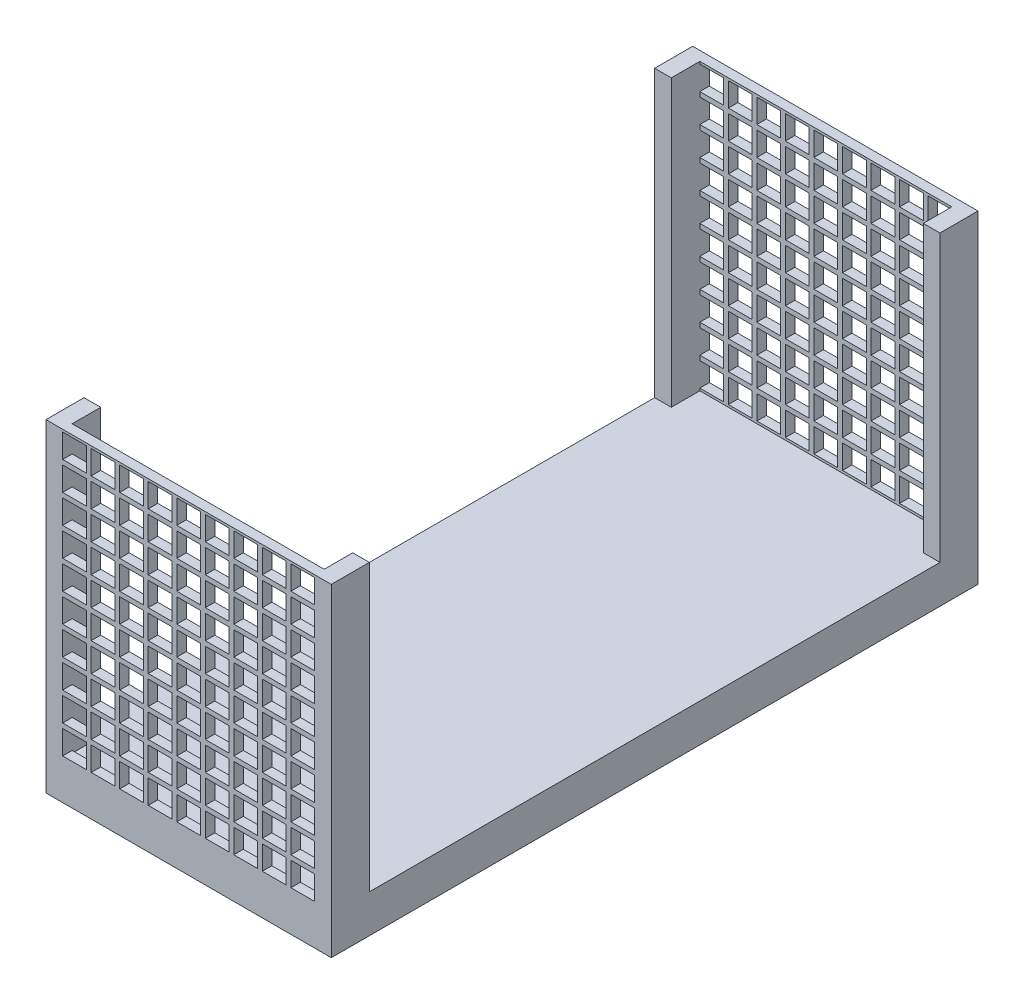
SolidWorks part; units mm, degrees
ref_plane "Front Plane" through (0, 0, 0) normal (0, 0, 1) x (1, 0, 0)
ref_plane "Top Plane" through (0, 0, 0) normal (0, 1, 0) x (1, 0, 0)
ref_plane "Right Plane" through (0, 0, 0) normal (1, 0, 0) x (0, 0, -1)
sketch "Sketch1" plane through (0, 0, 0) normal (0, 0, 1) x (1, 0, 0)
  line L1 (7.5, -8.5) -> (-7.5, -8.5)
  line L2 (7.5, -8.5) -> (7.5, 8.5)
  line L3 (7.5, 8.5) -> (-7.5, 8.5)
  line L4 (-7.5, -8.5) -> (-7.5, 8.5)
  line L5 (7.5, -8.5) -> (-7.5, 8.5) construction
  line L6 (7.5, 8.5) -> (-7.5, -8.5) construction
  point P0 (0, 0)
  dimension "D1" = 15
  dimension "D2" = 17
extrude "Boss-Extrude1" add sketch "Sketch1" along normal blind 34
sketch "Sketch2" plane through (7.5, 0, 0) normal (1, 0, 0) x (0, 0, -1)
  line L0 (-34, 8.5) -> (0, 8.5) construction
  line L1 (-32, 8.5) -> (-2, 8.5)
  line L2 (-32, 8.5) -> (-32, -6.5)
  line L3 (-32, -6.5) -> (-2, -6.5)
  line L4 (-2, 8.5) -> (-2, -6.5)
  line L5 (-34, -8.5) -> (-34, 8.5) construction
  line L6 (-34, -8.5) -> (0, -8.5) construction
  line L7 (0, -8.5) -> (0, 8.5) construction
  dimension "D1" = 2
  dimension "D2" = 2
  dimension "D3" = 2
extrude "Cut-Extrude1" cut sketch "Sketch2" against normal up to next
sketch "Sketch5" plane through (0, 0, 0) normal (0, 0, -1) x (-1, 0, 0)
  line L0 (-7.5, 8.5) -> (7.5, 8.5) construction
  line L1 (-6.625, 8.5) -> (6.625, 8.5)
  line L2 (-6.625, 8.5) -> (-6.625, -6.5)
  line L3 (-6.625, -6.5) -> (6.625, -6.5)
  line L4 (6.625, 8.5) -> (6.625, -6.5)
  line L5 (-6.625, 8.5) -> (-7.5, 8.5) construction
  line L6 (-7.5, 8.5) -> (6.625, 8.5) construction
  line L7 (-7.5, -8.5) -> (-7.5, 8.5) construction
  line L8 (6.625, 8.5) -> (7.5, 8.5) construction
  line L9 (7.5, -8.5) -> (-7.5, -8.5) construction
  dimension "D1" = 0.875
  dimension "D2" = 2
extrude "Cut-Extrude4" cut sketch "Sketch5" along normal blind 1.5 from surface at -2 starting at face at (0, 1, 2)
sketch "Sketch3" plane through (0, 0, 34) normal (0, 0, 1) x (1, 0, 0)
  line L0 (7.5, 8.5) -> (-7.5, 8.5) construction
  line L1 (-6.625, 8.5) -> (6.625, 8.5)
  line L2 (-6.625, 8.5) -> (-6.625, -6.5)
  line L3 (-6.625, -6.5) -> (6.625, -6.5)
  line L4 (6.625, 8.5) -> (6.625, -6.5)
  line L5 (-7.5, 8.5) -> (-7.5, -8.5) construction
  line L7 (-7.5, -8.5) -> (7.5, -8.5) construction
  line L8 (7.5, 8.5) -> (6.625, 8.5) construction
  line L9 (-6.625, 8.5) -> (-7.5, 8.5) construction
  dimension "D1" = 0.875
  dimension "D3" = 2
extrude "Cut-Extrude2" cut sketch "Sketch3" along normal blind 1.5 from surface at -2 starting at face at (0, 1, 32)
sketch "Sketch6" plane through (0, 0, 33.5) normal (0, 0, -1) x (-1, 0, 0)
  line L0 (-6.625, 8.375) -> (-6.625, 8.5) construction
  line L1 (-5.375, 7.125) -> (-6.625, 7.125)
  line L2 (-5.375, 7.125) -> (-5.375, 8.375)
  line L3 (-5.375, 8.375) -> (-6.625, 8.375)
  line L4 (-6.625, 7.125) -> (-6.625, 8.375)
  line L5 (-5.375, 7.125) -> (-6.625, 8.375) construction
  line L6 (-5.375, 8.375) -> (-6.625, 7.125) construction
  line L7 (-6.625, 8.5) -> (6.625, 8.5) construction
  line L8 (-6.625, -6.5) -> (-6.625, 8.5) construction
  point P0 (-6, 7.75)
  dimension "D1" = 1.25
  dimension "D2" = 0.125
extrude "Cut-Extrude5" cut sketch "Sketch6" along normal through all from surface at -0.5 starting at face at (0, 0, 34)
pattern_linear "LPattern1" count 9 spacing 1.5 along (-1, 0, 0) count 10 spacing 1.5 along (0, -1, 0) of "Cut-Extrude5"
